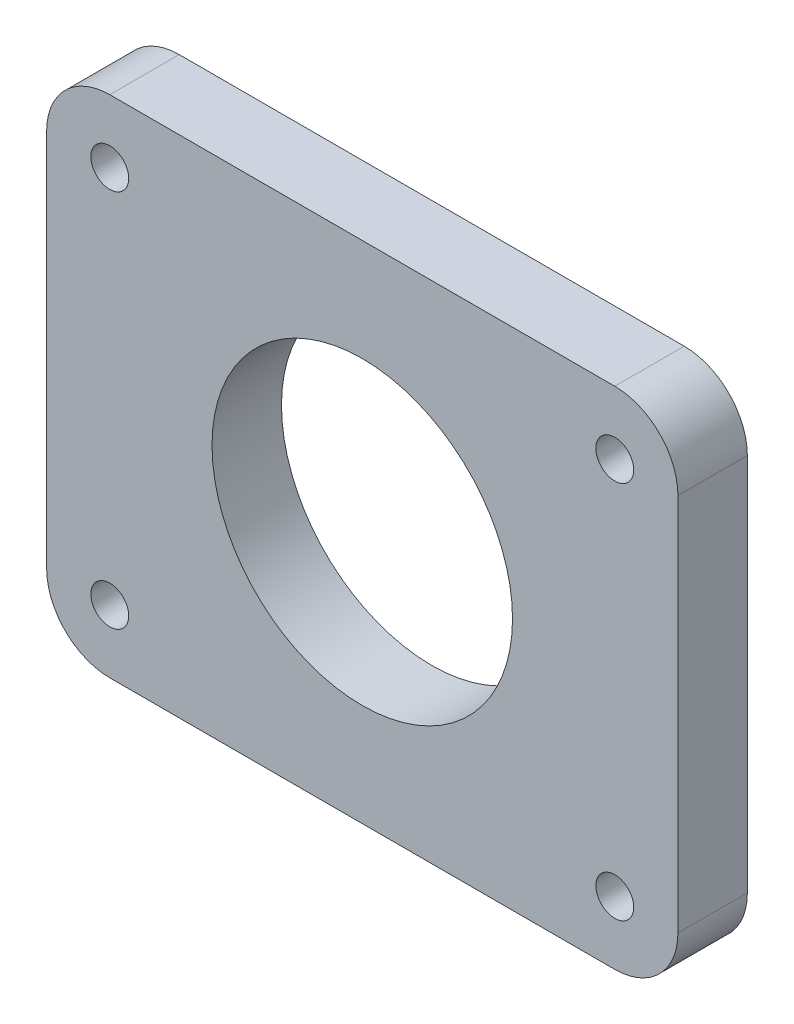
SolidWorks part; units mm, degrees
ref_plane "Alzado" through (0, 0, 0) normal (0, 0, 1) x (1, 0, 0)
ref_plane "Planta" through (0, 0, 0) normal (0, 1, 0) x (1, 0, 0)
ref_plane "Vista lateral" through (0, 0, 0) normal (1, 0, 0) x (0, 0, -1)
sketch "Croquis1" plane through (0, 0, 0) normal (0, 0, 1) x (1, 0, 0)
  line L0 (-20, 20) -> (20, 20)
  line L1 (-20, 15) -> (20, 15) construction
  line L2 (-20, 15) -> (-20, -15) construction
  line L3 (-20, -15) -> (20, -15) construction
  line L4 (20, 15) -> (20, -15) construction
  line L5 (-20, 15) -> (20, -15) construction
  line L6 (-20, -15) -> (20, 15) construction
  line L7 (25, 15) -> (25, -15)
  line L8 (-20, -20) -> (20, -20)
  line L9 (-25, 15) -> (-25, -15)
  line L10 (-25, -20) -> (25, -20) construction
  line L11 (-25, 20) -> (-25, -20) construction
  line L12 (25, 20) -> (25, -20) construction
  line L13 (-25, 20) -> (25, 20) construction
  circle A0 centre (-20, 15) radius 1.5
  circle A1 centre (0, 0) radius 11.9
  circle A2 centre (-20, -15) radius 1.5
  circle A3 centre (20, -15) radius 1.5
  circle A4 centre (20, 15) radius 1.5
  arc A5 (-20, -20) -> (-25, -15) centre (-20, -15) cw
  arc A6 (25, -15) -> (20, -20) centre (20, -15) cw
  arc A7 (20, 20) -> (25, 15) centre (20, 15) cw
  arc A8 (-20, 20) -> (-25, 15) centre (-20, 15) ccw
  point P0 (0, 0)
  dimension "D3" = 3
  dimension "D4" = 23.8
  dimension "D6" = 5
  dimension "D1" = 40
  dimension "D2" = 30
  dimension "D5" = 5
extrude "Saliente-Extruir1" add sketch "Croquis1" along normal blind 5.5
sketch "Croquis2" plane through (0, 0, 5.5) normal (0, 0, 1) x (1, 0, 0)
  line L0 (-25, 15) -> (-25, -15) construction
  line L1 (-25, 15) -> (-25, -15)
  line L2 (25, -15) -> (25, 15) construction
  line L3 (-20, -20) -> (20, -20) construction
  line L4 (20, 20) -> (-20, 20) construction
  line L5 (25, -15) -> (25, 15)
  line L6 (-20, -20) -> (20, -20)
  line L7 (20, 20) -> (-20, 20)
  circle A0 centre (20, 15) radius 1.5 construction
  circle A1 centre (20, -15) radius 1.5 construction
  circle A2 centre (0, 0) radius 11.9 construction
  circle A3 centre (-20, -15) radius 1.5 construction
  circle A4 centre (-20, 15) radius 1.5 construction
  circle A5 centre (20, 15) radius 1.5
  circle A6 centre (20, -15) radius 1.5
  circle A7 centre (0, 0) radius 11.9
  circle A8 centre (-20, -15) radius 1.5
  circle A9 centre (-20, 15) radius 1.5
  arc A10 (25, 15) -> (20, 20) centre (20, 15) ccw construction
  arc A11 (20, -20) -> (25, -15) centre (20, -15) ccw construction
  arc A12 (-25, -15) -> (-20, -20) centre (-20, -15) ccw construction
  arc A13 (-20, 20) -> (-25, 15) centre (-20, 15) ccw construction
  arc A14 (25, 15) -> (20, 20) centre (20, 15) ccw
  arc A15 (20, -20) -> (25, -15) centre (20, -15) ccw
  arc A16 (-25, -15) -> (-20, -20) centre (-20, -15) ccw
  arc A17 (-20, 20) -> (-25, 15) centre (-20, 15) ccw
